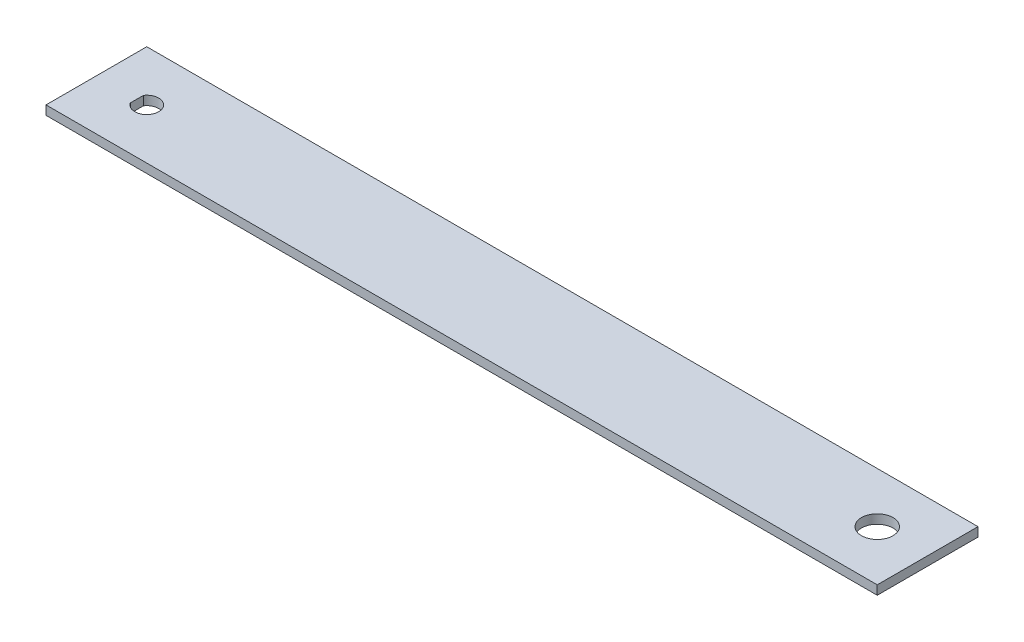
SolidWorks part; units mm, degrees
ref_plane "Front Plane" through (0, 0, 0) normal (0, 0, 1) x (1, 0, 0)
ref_plane "Top Plane" through (0, 0, 0) normal (0, 1, 0) x (1, 0, 0)
ref_plane "Right Plane" through (0, 0, 0) normal (1, 0, 0) x (0, 0, -1)
sketch "Sketch1" plane through (0, 0, 0) normal (0, 1, 0) x (1, 0, 0)
  line L1 (0, 0) -> (209.55, 0)
  line L2 (0, 0) -> (0, 25.4)
  line L3 (0, 25.4) -> (209.55, 25.4)
  line L4 (209.55, 0) -> (209.55, 25.4)
  dimension "D1" = 209.55
  dimension "D2" = 25.4
extrude "Boss-Extrude1" add sketch "Sketch1" along normal blind 2.286
sketch "Sketch2" plane through (0, 2.286, 0) normal (0, 1, 0) x (1, 0, 0)
  line L0 (0, 25.4) -> (0, 0) construction
  line L1 (10.2, 14.3583) -> (10.2, 11.0417)
  line L2 (209.55, 0) -> (209.55, 25.4) construction
  circle A1 centre (196.85, 12.7) radius 3.9687
  arc A2 (10.2, 11.0417) -> (10.2, 14.3583) centre (12.7, 12.7) ccw
  point P1 (11.1251, 12.7)
  point P8 (0, 12.7)
  point P9 (9.5099, 12.7)
  point P10 (15.7, 12.7)
  point P11 (0, 0)
  dimension "D1" = 6
  dimension "D2" = 5.5
  dimension "D3" = 184.15
  dimension "D4" = 7.9375
  dimension "D6" = 12.7
  dimension "D5" = 12.7
extrude "Cut-Extrude1" cut sketch "Sketch2" against normal through all
